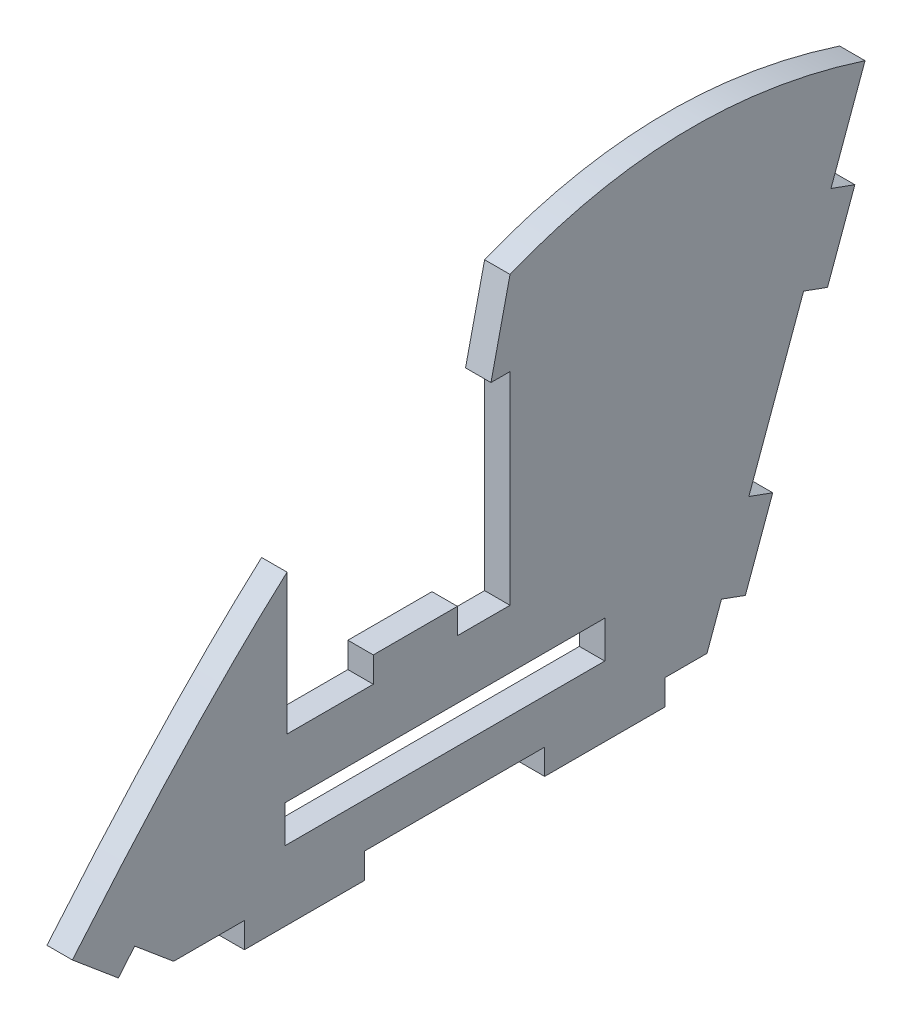
SolidWorks part; units mm, degrees
ref_plane "Front Plane" through (0, 0, 0) normal (0, 0, 1) x (1, 0, 0)
ref_plane "Top Plane" through (0, 0, 0) normal (0, 1, 0) x (1, 0, 0)
ref_plane "Right Plane" through (0, 0, 0) normal (1, 0, 0) x (0, 0, -1)
sketch "Sketch1" plane through (0, 0, 0) normal (1, 0, 0) x (0, 0, -1)
  line L0 (0, 0) -> (70, 0)
  line L1 (70, 0) -> (90.5212, 56.3816)
  line L2 (0, 0) -> (-11.4907, 9.6418)
  line L3 (132.6983, 41.0304) -> (48.3441, 71.7328) construction
  line L4 (16.7294, 43.2732) -> (-39.7107, -23.9895) construction
  spline S0 degree 3 poles (-11.4907, 9.6418) (19.4561, 46.5227) (48.0161, 71.8522) (90.5212, 56.3816) knots 0 0 0 0 1 1 1 1
  dimension "D1" = 70
  dimension "D2" = 110
  dimension "D3" = 60
  dimension "D4" = 140
  dimension "D5" = 15
extrude "Boss-Extrude1" add sketch "Sketch1" along normal blind 3.175 contours L2 S0 L1 L0
sketch "Sketch2" plane through (0, 0, 0) normal (-1, 0, 0) x (0, 0, 1)
  line L0 (0, 0) -> (-70, 0) construction
  line L1 (-43.175, 56.4665) -> (-15.325, 56.4665)
  line L2 (-43.175, 56.4665) -> (-43.175, 20.675)
  line L3 (-43.175, 20.675) -> (-15.325, 20.675)
  line L4 (-15.325, 56.4665) -> (-15.325, 20.675)
  spline S0 degree 3 poles (11.4907, 9.6418) (-19.4561, 46.5227) (-48.0161, 71.8522) (-90.5212, 56.3816) knots 0 0 0 0 1 1 1 1 construction
  dimension "D1" = 20.675
  dimension "D2" = 26.825
  dimension "D3" = 15.325
extrude "Cut-Extrude1" cut sketch "Sketch2" against normal through all
sketch "Sketch3" plane through (0, 0, 0) normal (-1, 0, 0) x (0, 0, 1)
  line L0 (-43.175, 20.675) -> (-15.325, 20.675) construction
  line L1 (-36.604, 20.675) -> (-26.096, 20.675)
  line L2 (-36.604, 20.675) -> (-36.604, 23.85)
  line L3 (-36.604, 23.85) -> (-26.096, 23.85)
  line L4 (-26.096, 20.675) -> (-26.096, 23.85)
  line L5 (-43.175, 56.4665) -> (-40.7938, 45.9585)
  line L6 (-43.175, 56.4665) -> (-43.175, 20.675) construction
  line L7 (-40.7938, 45.9585) -> (-43.175, 45.9585)
  line M5 (-15.325, 20.675) -> (-43.175, 20.675)
  line M6 (-43.175, 20.675) -> (-43.175, 56.4665)
  dimension "D1" = 10.508
  dimension "D2" = 6.571
  dimension "D3" = 3.175
  dimension "D4" = 2.3813
  dimension "D5" = 10.508
extrude "Boss-Extrude2" add sketch "Sketch3" against normal up to surface (3.175 mm away) contours L7 L5 M6 | L4 L3 L2 M5 up to face at (3.175, 23.4745, -28.6187)
sketch "Sketch4" plane through (0, 0, 0) normal (-1, 0, 0) x (0, 0, 1)
  line L0 (-83.2624, 45.7213) -> (-86.246, 44.6354)
  line L1 (-70, 0) -> (-90.5212, 56.3816) construction
  line L2 (-86.246, 44.6354) -> (-90.5212, 56.3816)
  line L3 (-90.5212, 56.3816) -> (-87.5377, 57.4675)
  line L4 (-87.5377, 57.4675) -> (-83.2624, 45.7213)
  line L5 (-79.8422, 36.3244) -> (-73.0018, 17.5305)
  line L6 (-73.0018, 17.5305) -> (-75.9854, 16.4446)
  line L7 (-75.9854, 16.4446) -> (-82.8258, 35.2385)
  line L8 (-82.8258, 35.2385) -> (-79.8422, 36.3244)
  line L9 (-72.5652, 7.0477) -> (-70, 0)
  line L10 (-70, 0) -> (-62.5, 0)
  line L11 (0, 0) -> (-70, 0) construction
  line L12 (-62.5, 0) -> (-62.5, 3.175)
  line L13 (-62.5, 3.175) -> (-67.7768, 3.175)
  line L14 (-67.7768, 3.175) -> (-69.5816, 8.1336)
  line L15 (-47.5, 3.175) -> (-25, 3.175)
  line L16 (-25, 3.175) -> (-25, 0)
  line L17 (-25, 0) -> (-47.5, 0)
  line L18 (-47.5, 0) -> (-47.5, 3.175)
  line L19 (-10, 3.175) -> (-10, 0)
  line L20 (-10, 0) -> (0, 0)
  line L21 (0, 0) -> (5.7453, 4.8209)
  line L22 (0, 0) -> (11.4907, 9.6418) construction
  line L23 (5.7453, 4.8209) -> (3.7045, 7.2531)
  line L24 (3.7045, 7.2531) -> (-1.1556, 3.175)
  line L25 (-1.1556, 3.175) -> (-10, 3.175)
  line L26 (-69.5816, 8.1336) -> (-72.5652, 7.0477)
  line L27 (-25, 0) -> (-47.5, 0)
  line L28 (-10, 0) -> (0, 0)
  spline M5 degree 3 poles (11.4907, 9.6418) (-19.4561, 46.5227) (-48.0161, 71.8522) (-90.5212, 56.3816) knots 0 0 0 0 1 1 1 1 only from (-43.175, 56.4665) to (-90.5212, 56.3816)
  line M6 (-90.5212, 56.3816) -> (-70, 0)
  line M7 (-70, 0) -> (0, 0)
  line M8 (0, 0) -> (11.4907, 9.6418)
extrude "Cut-Extrude2" cut sketch "Sketch4" against normal through all contours L4 L0 M5 M6 | L8 L6 L5 M6 | L18 L16 L15 M7 | L24 L25 L19 L23 M7 M8 | L14 L26 L9 L10 L12 L13
sketch "Sketch5" plane through (0, 0, 0) normal (-1, 0, 0) x (0, 0, 1)
  line L1 (-55.0096, 13.3695) -> (-15.0774, 13.3695)
  line L2 (-55.0096, 13.3695) -> (-55.0096, 8.7253)
  line L3 (-55.0096, 8.7253) -> (-15.0774, 8.7253)
  line L4 (-15.0774, 13.3695) -> (-15.0774, 8.7253)
extrude "Cut-Extrude3" cut sketch "Sketch5" against normal blind 10
